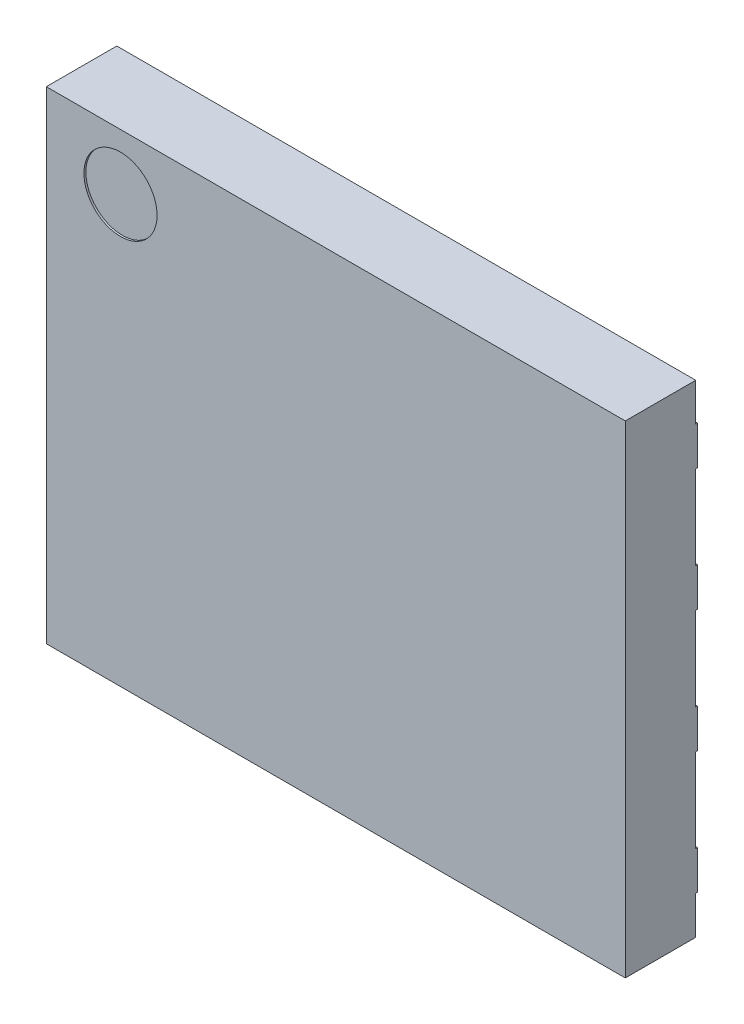
SolidWorks part; units mm, degrees
ref_plane "Front Plane" through (0, 0, 0) normal (0, 0, 1) x (1, 0, 0)
ref_plane "Top Plane" through (0, 0, 0) normal (0, 1, 0) x (1, 0, 0)
ref_plane "Right Plane" through (0, 0, 0) normal (1, 0, 0) x (0, 0, -1)
sketch "Sketch1" plane through (0, 0, 0) normal (0, 0, 1) x (1, 0, 0)
  line L1 (-3, -2.5) -> (3, -2.5)
  line L2 (-3, -2.5) -> (-3, 2.5)
  line L3 (-3, 2.5) -> (3, 2.5)
  line L4 (3, -2.5) -> (3, 2.5)
  line L5 (0, 2.5) -> (0, -2.5) construction
  line L6 (-3, 0) -> (3, 0) construction
  point P0 (0, 0)
  dimension "D1" = 6
  dimension "D2" = 5
extrude "Boss-Extrude1" add sketch "Sketch1" along normal blind 0.73 from offset 0.02
sketch "Sketch2" plane through (0, 0, 0) normal (0, 0, 1) x (1, 0, 0)
  line L1 (-1.7, -2.15) -> (1.7, -2.15)
  line L2 (-1.7, -2.15) -> (-1.7, 1.55)
  line L3 (-1.1, 2.15) -> (1.7, 2.15)
  line L4 (1.7, -2.15) -> (1.7, 2.15)
  line L5 (0, 2.15) -> (0, -2.15) construction
  line L6 (-1.7, 0) -> (1.7, 0) construction
  line L7 (-1.7, 1.55) -> (-1.1, 2.15)
  point P0 (0, 0)
  point P4 (-1.7, 2.15)
  dimension "D1" = 3.4
  dimension "D2" = 4.3
extrude "Boss-Extrude2" add sketch "Sketch2" along normal up to surface (0.02 mm away) up to face at (0, 0, 0.02)
sketch "Sketch3" plane through (0, 0, 0) normal (0, 0, 1) x (1, 0, 0)
  line L0 (-3, 1.905) -> (-2.4, 1.905) construction
  line L1 (-3, 2.5) -> (-3, -2.5) construction
  line L2 (-3, 2.105) -> (-2.4, 2.105)
  line L3 (-3, 1.705) -> (-2.4, 1.705)
  line L4 (-3, 2.105) -> (-3, 1.705)
  arc A1 (-2.4, 1.705) -> (-2.4, 2.105) centre (-2.4, 1.905) ccw
  point P4 (-2.7, 1.905)
  dimension "D1" = 0.4
  dimension "D2" = 1.905
  dimension "D3" = 0.6
extrude "Boss-Extrude3" add sketch "Sketch3" along normal up to surface (0.02 mm away) up to face at (-0.22, 0.31, 0.02)
pattern_linear "LPattern1" count 4 spacing 1.27 along (0, -1, 0) of "Boss-Extrude3"
mirror "Mirror1" about plane through (0, 0, 0) normal (1, 0, 0) of "LPattern1", "Boss-Extrude3"
sketch "Sketch4" plane through (0, 0, 0.75) normal (0, 0, 1) x (1, 0, 0)
  circle A0 centre (-2.2317, 1.9183) radius 0.3788
extrude "Cut-Extrude1" cut sketch "Sketch4" against normal blind 0.02 contours A0
